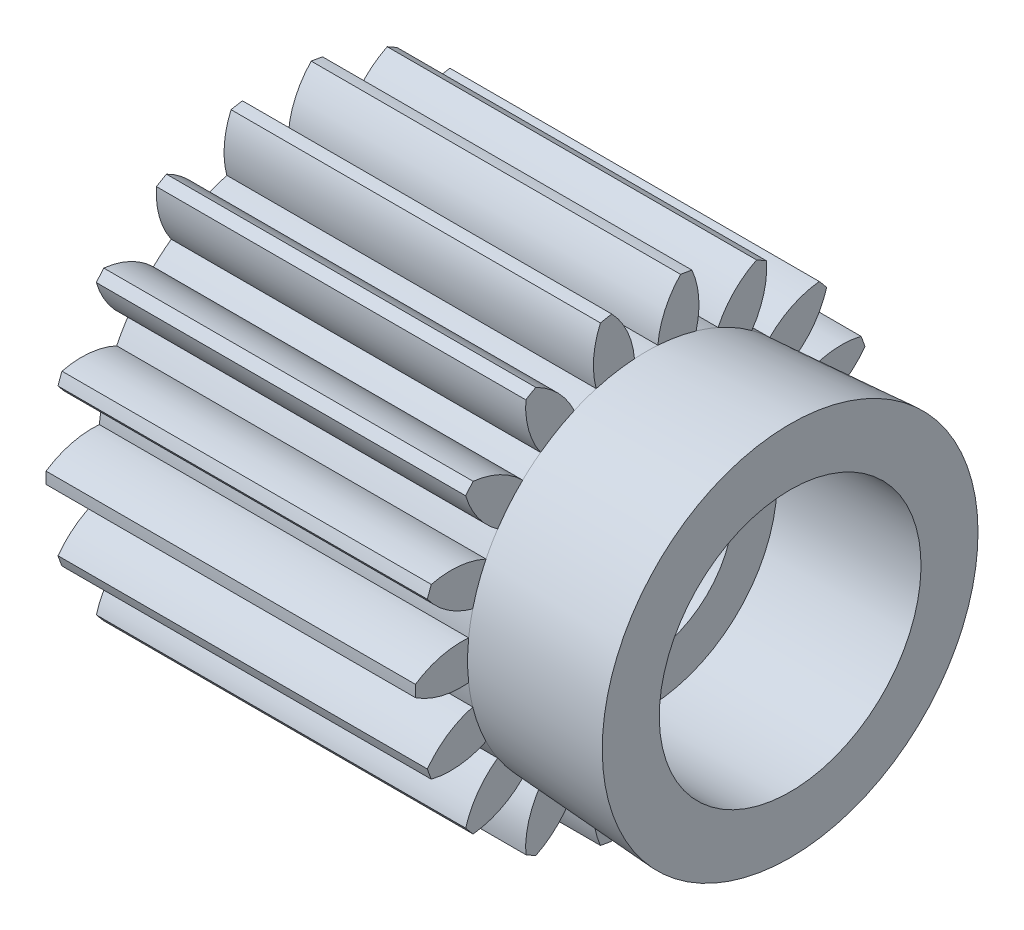
SolidWorks part; units mm, degrees
ref_plane "Plane1" through (0, 0, 0) normal (0, 0, 1) x (1, 0, 0)
ref_plane "Plane2" through (0, 0, 0) normal (0, 1, 0) x (1, 0, 0)
ref_plane "Plane3" through (0, 0, 0) normal (1, 0, 0) x (0, 0, -1)
sketch "HoldingSke" plane through (0, 0, 0) normal (0, 1, 0) x (1, 0, 0)
  line L0 (0, 0) -> (773.0187, -251.169)
  line L1 (-15, 0) -> (100, 0) construction
  line L2 (0, 0) -> (-2.1039, 2.3779)
  line L3 (0, 0) -> (-11.863, 4.5341)
  line L4 (0, 0) -> (8.2133, 2.6687)
  line L5 (0, 0) -> (-47.5972, -17.7524)
  line L6 (0, 0) -> (-10.5278, -7.1032)
  line L7 (-2.1039, 2.3779) -> (8.8308, 51.9871)
  line L8 (-76.2, 54.61) -> (-69.596, 54.61)
  line L9 (-71.009, 38.7566) -> (-53.1078, 45.2721)
  line L10 (-76.2, 71.12) -> (104.1128, 71.12)
  line L11 (0, 0) -> (-12.7, 0)
  line L12 (-76.2, 101.6) -> (-76.1716, 101.6)
  line L13 (24.9733, 27.94) -> (52.9518, 28.4284)
  line L14 (24.9733, 27.94) -> (25.0241, 27.9398)
  line L15 (24.9733, 27.94) -> (100.4021, 29.52)
  circle A0 centre (0, 0) radius 3.175
  circle A1 centre (0, 0) radius 6.1404
  circle A2 centre (0, 0) radius 38.1
  circle A3 centre (0, 0) radius 3.175
  dimension "MHD" = 12.2809
  dimension "Hub_dia" = 76.2
  dimension "Bore" = 6.35
  dimension "MBD" = 6.35
  dimension "Num_teeth" = 18
  dimension "Pitch" = 812.8
  dimension "Overall_len" = 50.8
  dimension "Show_teeth" = 18
  dimension "Thickness" = 12.7
  dimension "OAL" = 50.8001
  dimension "T_dim" = 6.604
  dimension "Ap" = 20
  dimension "H" = 19.05
  dimension "Pitch_radius" = 180.3128
  dimension "Width" = 12.7
  dimension "Backlash" = 0.0284
  dimension "Addendum_fac" = 1
  dimension "Dedendum_fac" = 1.2
  dimension "Clearance_fac" = 0.2
  dimension "Dedendum_add" = 0.0508
sketch "BasProSke" plane through (0, 0, 0) normal (0, 1, 0) x (1, 0, 0)
  line L0 (-10, 0) -> (60, 0) construction
  line L1 (0, 0) -> (0, 7.9375)
  line L2 (0, 0) -> (12.7, 0)
  line L3 (12.7, 0) -> (12.7, 7.9375)
  line L4 (12.7, 7.9375) -> (0, 7.9375)
  dimension "Thickness" = 12.7
  dimension "Diameter" = 15.875
revolve "Base-Revolve" add sketch "BasProSke" angle 360 about L0
sketch "TooCutSke" plane through (0, 0, 0) normal (1, 0, 0) x (0, 0, -1)
  line L1 (0, 0) -> (0, 107) construction
  line L2 (0, 0) -> (-0.6724, 7.112) construction
  line L3 (0, 0) -> (-2.473, 14.0251) construction
  line L4 (-0.6724, 7.112) -> (-1.2365, 7.0126) construction
  arc A0 (0.4018, 6.1273) -> (-0.4018, 6.1273) centre (0, 0) ccw
  arc A1 (1.2039, 7.8714) -> (-1.2039, 7.8714) centre (0, 0) ccw
  circle A2 centre (0, 0) radius 7.1438 construction
  circle A3 centre (0, 0) radius 6.7129 construction
  arc A4 (-0.4018, 6.1273) -> (-1.2039, 7.8714) centre (-3.2481, 5.8748) ccw
  arc A5 (1.2039, 7.8714) -> (0.4018, 6.1273) centre (3.2481, 5.8748) ccw
  dimension "Root_dia" = 12.2809
  dimension "Overcut_dia" = 15.9258
  dimension "Pitch_dia" = 14.2875
  dimension "Base_dia" = 13.4259
  dimension "Flank_rad" = 2.8575
  dimension "Half_ang" = 10
  dimension "Half_CT" = 0.5728
extrude "ToothCut" cut sketch "TooCutSke" along normal through all
fillet "Breaks" [suppressed] radius 0.0159
fillet "RootFillets" [suppressed] radius 0.2095
pattern_circular "TeethCuts" count 18 every 20 about axis through (-10, 0, 0) along (1, 0, 0) of "ToothCut", "RootFillets", "Breaks"
sketch "HubNeaOneSke" plane through (0, 0, 0) normal (-1, 0, 0) x (0, 0, 1)
  circle A0 centre (0, 0) radius 6.1404
  dimension "Diameter" = 12.2809
extrude "HubNearOne" [suppressed] add sketch "HubNeaOneSke" along normal blind 38.1001
sketch "HubNeaBotSke" plane through (0, 0, 0) normal (-1, 0, 0) x (0, 0, 1)
  circle A0 centre (0, 0) radius 6.1404
  dimension "Diameter" = 12.2809
extrude "HubNearBoth" [suppressed] add sketch "HubNeaBotSke" along normal blind 19.05
ref_plane "FarPln" through (12.7, 0, 0) normal (1, 0, 0) x (0, 0, -1)
sketch "HubFarSke" plane through (12.7, 0, 0) normal (1, 0, 0) x (0, 0, -1)
  circle A0 centre (0, 0) radius 6.1404
  dimension "Diameter" = 12.2809
extrude "HubFar" [suppressed] add sketch "HubFarSke" along normal blind 19.05
sketch "BorSke" plane through (0, 0, 0) normal (1, 0, 0) x (0, 0, -1)
  circle A0 centre (0, 0) radius 3
  dimension "D1" = 6
extrude "Bore" cut sketch "BorSke" along normal mid plane 101.6001
sketch "KeySke" plane through (0, 0, 0) normal (1, 0, 0) x (0, 0, -1)
  line L0 (-0.127, 0) -> (-0.127, 3.429)
  line L1 (-0.127, 3.429) -> (0.127, 3.429)
  line L2 (0.127, 3.429) -> (0.127, 0)
  line L3 (0, 0) -> (0, 34) construction
  line L4 (-0.127, 0) -> (0.127, 0)
  dimension "Offset" = 3.429
  dimension "Width" = 0.254
extrude "Keyway" [suppressed] cut sketch "KeySke" along normal mid plane 101.6001
pattern_circular "Keyway2" [suppressed] count 2 every 90 about axis through (-10, 0, 0) along (1, 0, 0)
sketch "Sketch1" plane through (0, 0, 0) normal (0, 0, 1) x (1, 0, 0)
  line L0 (12.7, 6.1405) -> (17.65, 6.46)
  line L1 (17.65, 6.46) -> (17.65, 4.46)
  line L2 (17.65, 4.46) -> (12.7, 4.46)
  line L3 (12.7, 4.9483) -> (12.7, 5.2527) construction
  line L4 (12.7, 0) -> (13.683, 0) construction
  line L5 (12.7, -0.1987) -> (12.7, 0.1987) construction
  line L6 (12.7, 4.46) -> (12.7, 6.1405)
  line L7 (12.7, 5.8952) -> (12.7, 7.78) construction
  dimension "D1" = 4.46
  dimension "D2" = 2
  dimension "D3" = 4.95
revolve "Revolve1" add sketch "Sketch1" angle 360 about L4
sketch "Sketch2" plane through (17.65, 0, 0) normal (1, 0, 0) x (0, 0, -1)
  circle A0 centre (0, 0) radius 4.5
extrude "Cut-Extrude1" cut sketch "Sketch2" against normal up to surface (4.95 mm away) up to face at (12.7, 0, 4.46)
equation "' \"Pitch@HoldingSke\" = 4"
equation "' \"Num_teeth@HoldingSke\" = 12"
equation "' \"Ap@HoldingSke\" =  20"
equation "' \"Ap@HoldingSke\" = 20"
equation "' \"Width@HoldingSke\" = 0.5"
equation "' \"Hub_dia@HoldingSke\"= 1"
equation "' \"Hub_dia@HoldingSke\" = 1"
equation "' \"Overall_len@HoldingSke\" = 1.0"
equation "' \"Bore@HoldingSke\" = 0.75"
equation "' \"T_dim@HoldingSke\" = 0.85"
equation "' \"Width@KeySke\" = 0.25"
equation "' \"Show_teeth@HoldingSke\" = 13"
equation "' \"Backlash@HoldingSke\" = 0.009"
equation "' \"Addendum_fac@HoldingSke\" = 1.0"
equation "' \"Dedendum_fac@HoldingSke\" = 1.25"
equation "' \"Dedendum_add@HoldingSke\" = 0.00005"
equation "' \"Clearance_fac@HoldingSke\" = 0.25"
equation "' \"Pitch@HoldingSke\" = 0.5"
equation "' \"Num_teeth@HoldingSke\" = 23"
equation "' \"Show_teeth@HoldingSke\" = 23"
equation "' \"Backlash@HoldingSke\" = 0.0375"
equation "\"Overcut_dia@TooCutSke\" = (\"Num_teeth@HoldingSke\" + 2 * \"Addendum_fac@HoldingSke\") / \"Pitch@HoldingSke\" + 0.002"
equation "\"Pitch_dia@TooCutSke\" = \"Num_teeth@HoldingSke\" / \"Pitch@HoldingSke\""
equation "\"Base_dia@TooCutSke\" = \"Num_teeth@HoldingSke\" / \"Pitch@HoldingSke\" * cos((\"Ap@HoldingSke\"  * 3.14159265 / 180))"
equation "\"Root_dia@TooCutSke\" = (\"Num_teeth@HoldingSke\" + 2) / \"Pitch@HoldingSke\" - 2 * (\"Addendum_fac@HoldingSke\" + \"Dedendum_fac@HoldingSke\") / \"Pitch@HoldingSke\" - \"Dedendum_add@HoldingSke\" * 2"
equation "\"Half_ang@TooCutSke\" = 180 / \"Num_teeth@HoldingSke\""
equation "\"Half_CT@TooCutSke\" = \"Num_teeth@HoldingSke\" / \"Pitch@HoldingSke\" * sin((3.14159265 / 2 / \"Num_teeth@HoldingSke\")) / 2 - 7 * \"Backlash@HoldingSke\" / 4"
equation "\"Flank_rad@TooCutSke\" = \"Num_teeth@HoldingSke\" / \"Pitch@HoldingSke\" / 5"
equation "\"Radius@RootFillets\" = \"Clearance_fac@HoldingSke\" / \"Pitch@HoldingSke\" + \"Dedendum_add@HoldingSke\""
equation "\"Break_rad@Breaks\" = 0.02 / \"Pitch@HoldingSke\""
equation "\"Thickness@HoldingSke\" = \"Width@HoldingSke\""
equation "\"OAL@HoldingSke\" = \"Thickness@HoldingSke\""
equation "\"MHD@HoldingSke\" = (\"Num_teeth@HoldingSke\" + 2) / \"Pitch@HoldingSke\" - 2 * (\"Addendum_fac@HoldingSke\" + \"Dedendum_fac@HoldingSke\")  / \"Pitch@HoldingSke\" - \"Dedendum_add@HoldingSke\" * 2"
equation "\"MBD@HoldingSke\" = (\"Num_teeth@HoldingSke\" + 2) / \"Pitch@HoldingSke\" - 2 * (\"Addendum_fac@HoldingSke\" + \"Dedendum_fac@HoldingSke\")  / \"Pitch@HoldingSke\" - \"Dedendum_add@HoldingSke\" * 2 - 0.002"
equation "\"MHD@HoldingSke\" = ((sgn( \"MHD@HoldingSke\" - \"Hub_dia@HoldingSke\" )-1)*( \"MHD@HoldingSke\" - \"Hub_dia@HoldingSke\" ))/-2+ \"Hub_dia@HoldingSke\""
equation "\"MBD@HoldingSke\" = ((sgn( \"MBD@HoldingSke\" - \"Bore@HoldingSke\" )-1)*( \"MBD@HoldingSke\" - \"Bore@HoldingSke\" ))/-2+ \"Bore@HoldingSke\""
equation "\"OAL@HoldingSke\" = ((sgn( \"OAL@HoldingSke\" - \"Overall_len@HoldingSke\" )+1)*( \"OAL@HoldingSke\" - \"Overall_len@HoldingSke\" ))/2 + \"Overall_len@HoldingSke\" + 0.000002"
equation "\"Num_teeth@TeethCuts\" = int( \"Show_teeth@HoldingSke\" ) + 1"
equation "\"Num_teeth@TeethCuts\" = ((sgn( \"Num_teeth@TeethCuts\" - \"Num_teeth@HoldingSke\" )-1)*( \"Num_teeth@TeethCuts\" - \"Num_teeth@HoldingSke\" ))/-2+ \"Num_teeth@HoldingSke\""
equation "\"Num_teeth@TeethCuts\" = ((sgn( \"Num_teeth@TeethCuts\" - 2.0)+1)*( \"Num_teeth@TeethCuts\" - 2.0))/2 +2.0"
equation "\"Angle@TeethCuts\" = 360.0 / \"Num_teeth@HoldingSke\""
equation "\"Diameter@BasProSke\" = (\"Num_teeth@HoldingSke\" + 2 * \"Addendum_fac@HoldingSke\") / \"Pitch@HoldingSke\""
equation "\"Thickness@BasProSke\"  = \"Thickness@HoldingSke\""
equation "' \"Fillet_rad@BasProSke\" =  \"Thickness@HoldingSke\" * 0.05"
equation "' \"Fillet_rad@BasProSke\" = \"Thickness@HoldingSke\" * 0.05"
equation "\"MHD@HoldingSke\" = ((sgn( \"MHD@HoldingSke\" - \"Root_dia@TooCutSke\" )-1)*( \"MHD@HoldingSke\" - \"Root_dia@TooCutSke\" ))/-2+ \"Root_dia@TooCutSke\""
equation "\"Diameter@HubNeaOneSke\" = \"MHD@HoldingSke\""
equation "\"Length@HubNearOne\" = \"OAL@HoldingSke\" - \"Thickness@BasProSke\""
equation "\"Diameter@HubNeaBotSke\" = \"MHD@HoldingSke\""
equation "\"Length@HubNearBoth\" = ( \"OAL@HoldingSke\" - \"Thickness@BasProSke\" ) / 2.0"
equation "\"Thickness@FarPln\" = \"Thickness@BasProSke\""
equation "\"Diameter@HubFarSke\" = \"MHD@HoldingSke\""
equation "\"Length@HubFar\" = ( \"OAL@HoldingSke\" - \"Thickness@BasProSke\" ) / 2.0"
equation "\"D1@Bore\" = \"OAL@HoldingSke\" * 2.0"
equation "\"D1@Keyway\" = \"OAL@HoldingSke\" * 2.0"
equation "\"Offset@KeySke\" = \"T_dim@HoldingSke\" - \"MBD@HoldingSke\" / 2.0"
